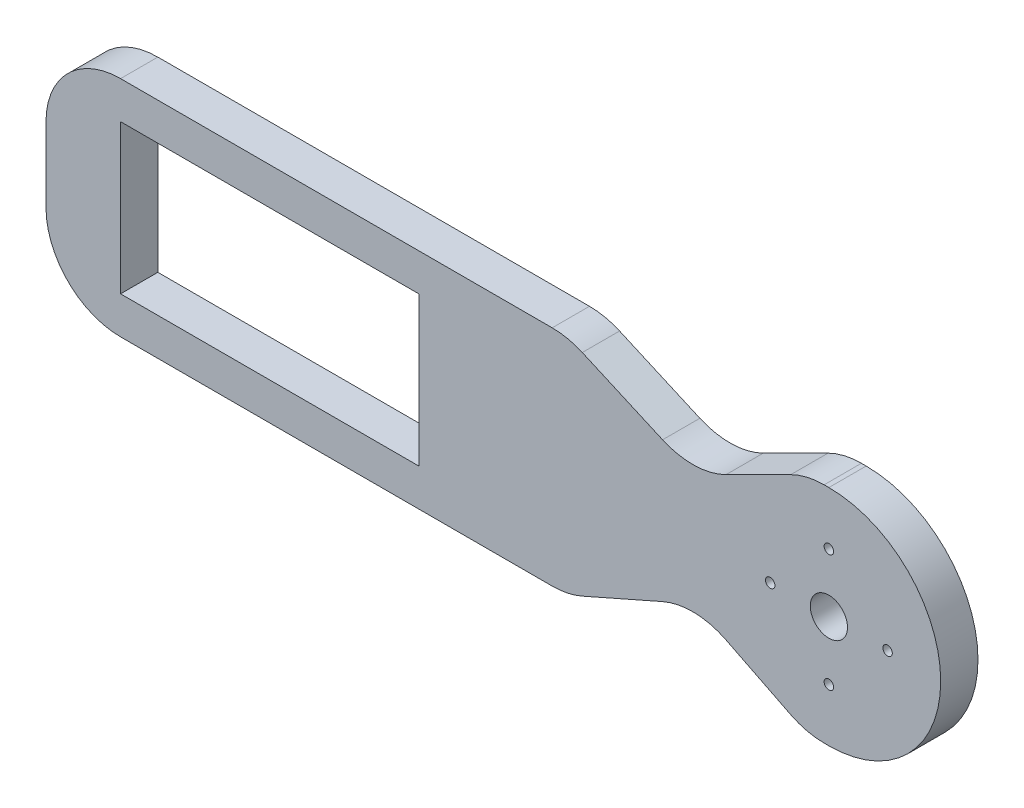
SolidWorks part; units mm, degrees
ref_plane "Front Plane" through (0, 0, 0) normal (0, 0, 1) x (1, 0, 0)
ref_plane "Top Plane" through (0, 0, 0) normal (0, 1, 0) x (1, 0, 0)
ref_plane "Right Plane" through (0, 0, 0) normal (1, 0, 0) x (0, 0, -1)
sketch "Sketch1" plane through (0, 0, 0) normal (0, 0, 1) x (1, 0, 0)
  line L1 (5, -0.0421) -> (-100, -0.0421)
  line L3 (5, 29.9579) -> (-100, 29.9579)
  line L4 (-100, -0.0421) -> (-100, 29.9579)
  line L5 (-90, 24.9579) -> (-50, 24.9579)
  line L6 (-90, 24.9579) -> (-90, 4.9579)
  line L7 (-90, 4.9579) -> (-50, 4.9579)
  line L8 (-50, 24.9579) -> (-50, 4.9579)
  arc A0 (5, -0.0421) -> (5, 29.9579) centre (5, 14.9579) ccw
  circle A1 centre (5, 14.9579) radius 2.5
  circle A2 centre (5, 22.8329) radius 0.635
  circle A3 centre (-2.875, 14.9579) radius 0.635
  circle A4 centre (12.875, 14.9579) radius 0.635
  circle A5 centre (5, 7.0829) radius 0.635
  dimension "D7" = 30
  dimension "D8" = 7.875
  dimension "D9" = 7.875
  dimension "D10" = 7.875
  dimension "D11" = 5
  dimension "D12" = 7.875
  dimension "D13" = 1.27
  dimension "D14" = 1.27
  dimension "D15" = 1.27
  dimension "D16" = 1.27
  dimension "D17" = 55
  dimension "D2" = 30
  dimension "D3" = 40
  dimension "D4" = 20
  dimension "D5" = 5
  dimension "D6" = 10
extrude "Boss-Extrude1" add sketch "Sketch1" along normal blind 5
sketch "Sketch2" plane through (0, 0, 5) normal (0, 0, 1) x (1, 0, 0)
  line L4 (-28.0715, 29.1071) -> (-17.3024, 24.3561)
  line L5 (5, 29.9579) -> (-100, 29.9579) construction
  line L6 (-8.7939, 24.561) -> (-0.1115, 28.9022)
  line L7 (-28.0715, 0.8088) -> (-17.3024, 5.5598)
  line L8 (-100, -0.0421) -> (5, -0.0421) construction
  line L9 (-8.7939, 5.3549) -> (-0.1115, 1.0137)
  line L10 (-100, 29.9579) -> (-100, -0.0421) construction
  line L15 (-32.1079, 29.9579) -> (4.3607, 29.9579)
  line L16 (-32.1079, -0.0421) -> (4.3607, -0.0421)
  arc A0 (-8.7939, 24.561) -> (-17.3024, 24.3561) centre (-13.266, 33.5053) cw
  arc A1 (-8.7939, 5.3549) -> (-17.3024, 5.5598) centre (-13.266, -3.5894) ccw
  arc A3 (-28.0715, 29.1071) -> (-32.1079, 29.9579) centre (-32.1079, 19.9579) ccw
  arc A4 (-28.0715, 0.8088) -> (-32.1079, -0.0421) centre (-32.1079, 9.9579) cw
  arc A5 (4.3607, -0.0421) -> (-0.1115, 1.0137) centre (4.3607, 9.9579) cw
  arc A6 (4.3607, 29.9579) -> (-0.1115, 28.9022) centre (4.3607, 19.9579) ccw
  point P15 (-13, 22.4579)
  point P18 (-13, 7.4579)
  point P26 (-40, 29.9579)
  point P29 (-40, -0.0421)
  point P32 (2, -0.0421)
  point P35 (2, 29.9579)
  dimension "D10" = 10
  dimension "D9" = 10
  dimension "D15" = 10
  dimension "D16" = 10
  dimension "D17" = 10
  dimension "D18" = 10
  dimension "D1" = 60
  dimension "D2" = 60
  dimension "D3" = 87
  dimension "D4" = 87
  dimension "D5" = 102
  dimension "D6" = 102
  dimension "D7" = 7.5
  dimension "D8" = 7.5
extrude "Cut-Extrude1" cut sketch "Sketch2" against normal blind 5
fillet "Fillet1" radius 10 1 edges at (-100, 29.9579, 2.5)
fillet "Fillet2" radius 10 1 edges at (-100, -0.0421, 2.5)
